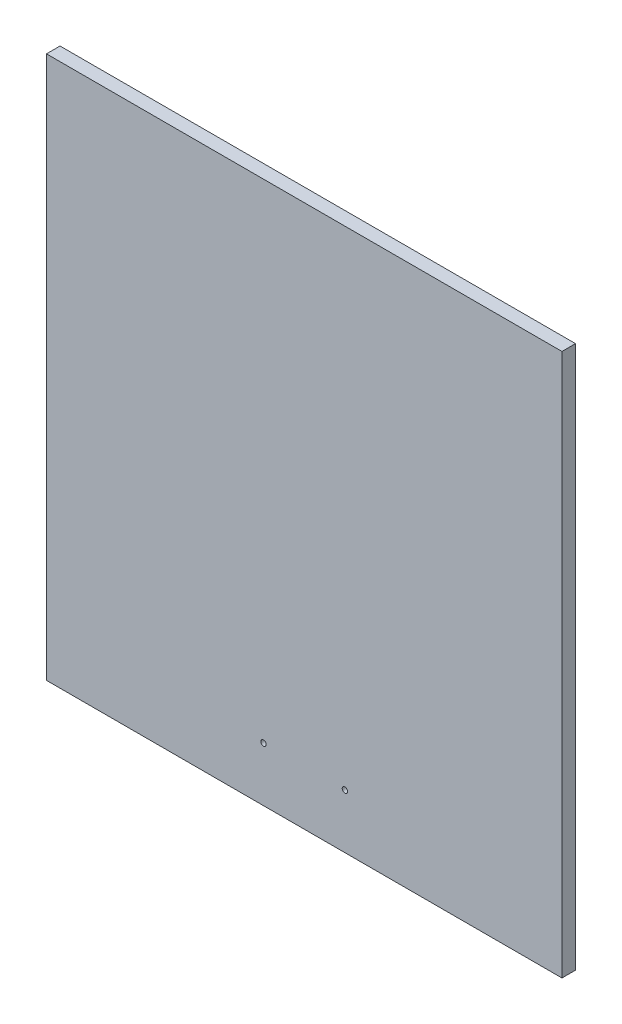
SolidWorks part; units mm, degrees
ref_plane "Front Plane" through (0, 0, 0) normal (0, 0, 1) x (1, 0, 0)
ref_plane "Top Plane" through (0, 0, 0) normal (0, 1, 0) x (1, 0, 0)
ref_plane "Right Plane" through (0, 0, 0) normal (1, 0, 0) x (0, 0, -1)
sketch "Croquis1" plane through (0, 0, 0) normal (0, 0, 1) x (1, 0, 0)
  line L1 (-95, -100) -> (95, -100)
  line L2 (-95, -100) -> (-95, 100)
  line L3 (-95, 100) -> (95, 100)
  line L4 (95, -100) -> (95, 100)
  line L5 (-95, -100) -> (95, 100) construction
  line L6 (-95, 100) -> (95, -100) construction
  point P0 (0, 0)
  dimension "D1" = 200
  dimension "D2" = 190
extrude "Saliente-Extruir1" add sketch "Croquis1" along normal blind 5
sketch "Croquis2" plane through (0, 0, 5) normal (0, 0, 1) x (1, 0, 0)
  line L0 (0, 0) -> (0, -100) construction
  line L1 (-95, -100) -> (95, -100) construction
  circle A0 centre (-15, -80) radius 1
  circle A1 centre (15, -80) radius 1
  dimension "D2" = 2
  dimension "D1" = 15
  dimension "D3" = 20
extrude "Cortar-Extruir1" cut sketch "Croquis2" against normal blind 10
